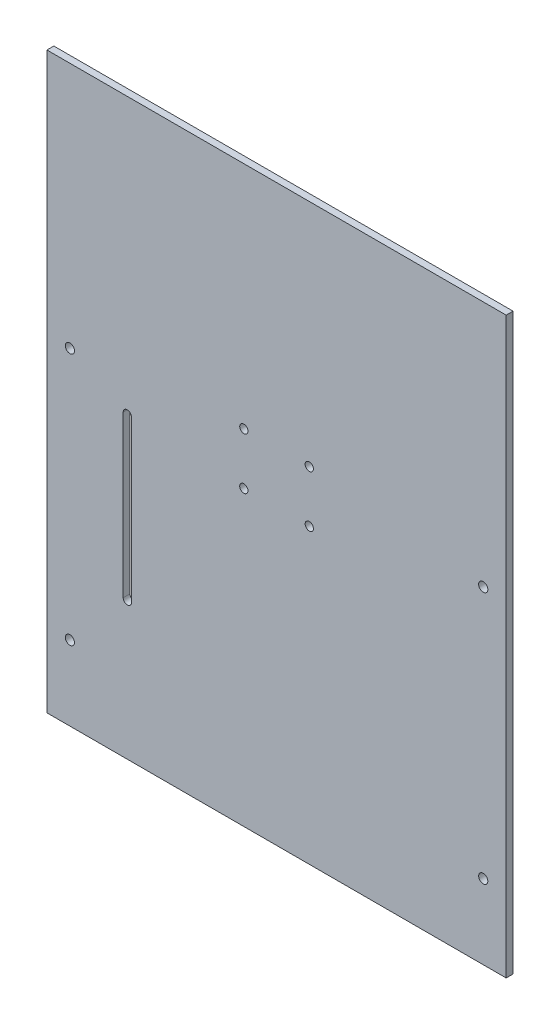
SolidWorks part; units mm, degrees
material "Balsa"
ref_plane "Plano frontal" through (0, 0, 0) normal (0, 0, 1) x (1, 0, 0)
ref_plane "Plano superior" through (0, 0, 0) normal (0, 1, 0) x (1, 0, 0)
ref_plane "Plano direito" through (0, 0, 0) normal (1, 0, 0) x (0, 0, -1)
sketch "Esboço1" plane through (0, 0, 0) normal (0, 0, 1) x (1, 0, 0)
  line L0 (-100, 125) -> (100, 125)
  line L1 (0, 0) -> (0, -105.1003) construction
  line L2 (-100, 125) -> (-100, -125)
  line L3 (-63.2, 5) -> (-63.2, -65)
  line L4 (100, 125) -> (100, -125)
  line L5 (-100, 125) -> (100, -125) construction
  line L6 (-100, -125) -> (100, 125) construction
  line L7 (-66.8, 5) -> (-66.8, -65)
  line L11 (-100, -125) -> (100, -125)
  line L13 (-14.25, 25) -> (14.25, 25) construction
  circle A0 centre (-14.25, 25) radius 1.8
  circle A1 centre (14.25, 25) radius 1.8
  circle A2 centre (14.25, 2.5) radius 1.8
  circle A3 centre (-14.25, 2.5) radius 1.8
  arc A4 (-63.2, 5) -> (-66.8, 5) centre (-65, 5) ccw
  arc A5 (-66.8, -65) -> (-63.2, -65) centre (-65, -65) ccw
  circle A6 centre (-90, -92.5) radius 2
  circle A7 centre (-90, 17.5) radius 2
  circle A8 centre (90, 17.5) radius 2
  circle A9 centre (90, -92.5) radius 2
  point P0 (0, 0)
  point P6 (0, -16.4394)
  point P7 (0, 125)
  point P15 (0, 25)
  point P33 (-60, -115)
  point P40 (60, -115)
  dimension "D6" = 3.6
  dimension "D9" = 35
  dimension "D11" = 3.6
  dimension "D16" = 4
  dimension "D1" = 200
  dimension "D2" = 250
  dimension "D5" = 100
  dimension "D7" = 28.5
  dimension "D8" = 22.5
  dimension "D10" = 130
  dimension "D12" = 70
  dimension "D13" = 110
  dimension "D14" = 32.5
  dimension "D15" = 10
  dimension "D19" = 40
  dimension "D20" = 10
  dimension "D3" = 2
  dimension "D4" = 2
extrude "Ressalto-extrusão1" add sketch "Esboço1" along normal blind 3
